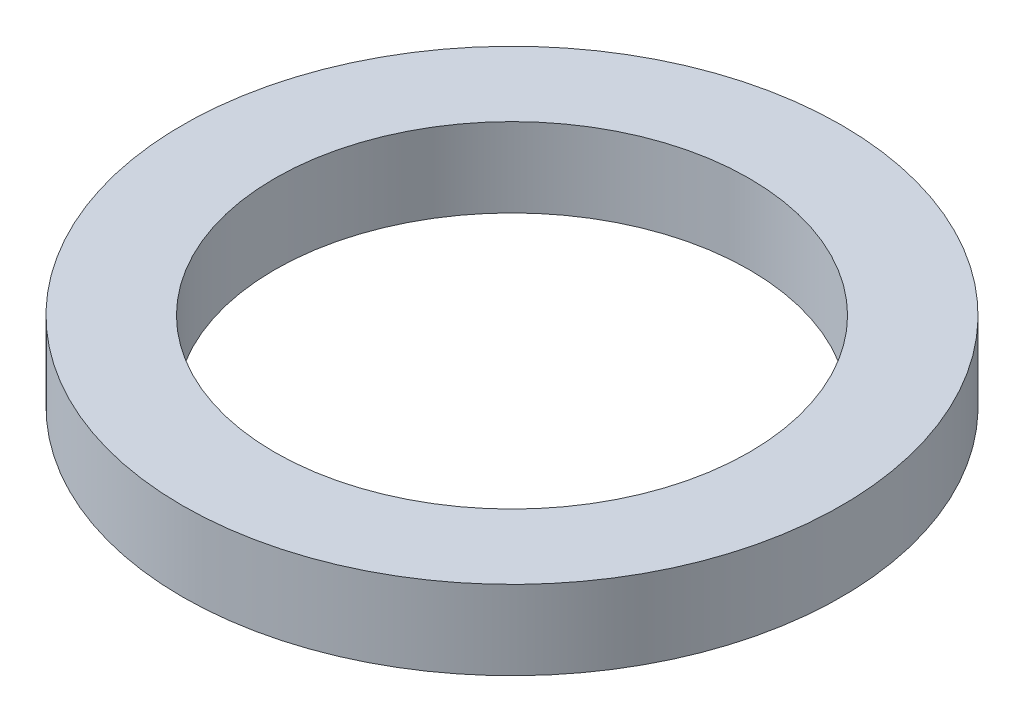
SolidWorks part; units mm, degrees
ref_plane "前视基准面" through (0, 0, 0) normal (0, 0, 1) x (1, 0, 0)
ref_plane "上视基准面" through (0, 0, 0) normal (0, 1, 0) x (1, 0, 0)
ref_plane "右视基准面" through (0, 0, 0) normal (1, 0, 0) x (0, 0, -1)
sketch "草图1" plane through (0, 0, 0) normal (0, 1, 0) x (1, 0, 0)
  circle A0 centre (0, 0) radius 3.6
  circle A1 centre (0, 0) radius 5
  dimension "D1" = 7.2
  dimension "D2" = 10
extrude "凸台-拉伸1" add sketch "草图1" along normal blind 1.2
